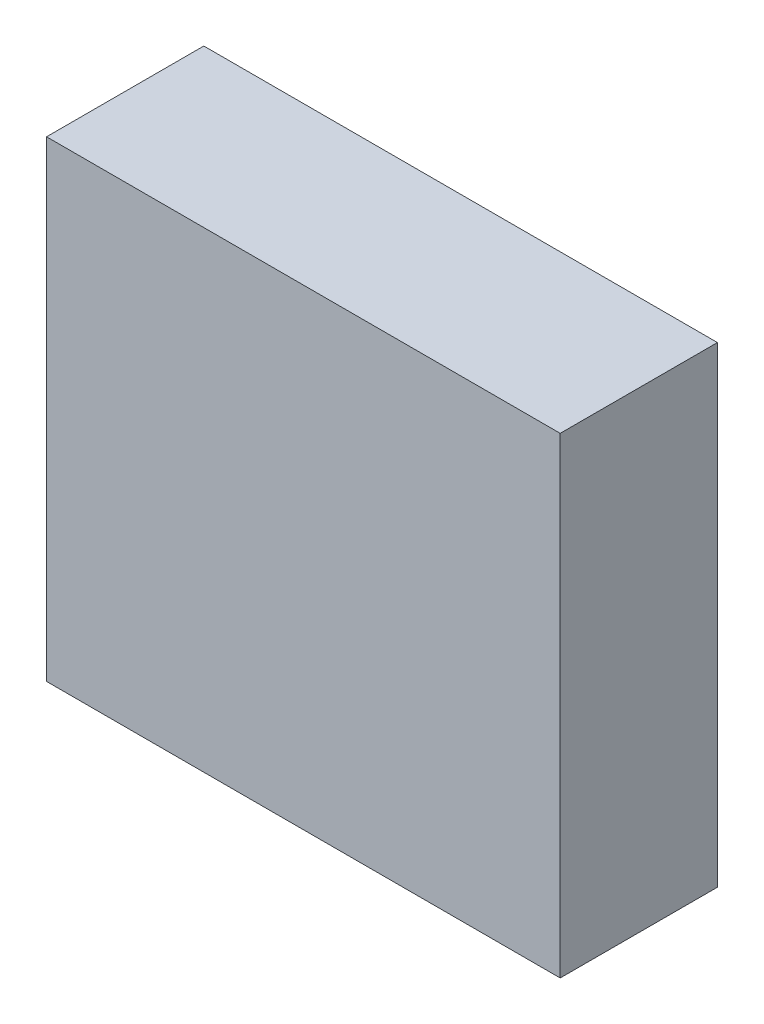
SolidWorks part; units mm, degrees
ref_plane "Plan de face" through (0, 0, 0) normal (0, 0, 1) x (1, 0, 0)
ref_plane "Plan de dessus" through (0, 0, 0) normal (0, 1, 0) x (1, 0, 0)
ref_plane "Plan de droite" through (0, 0, 0) normal (1, 0, 0) x (0, 0, -1)
sketch "Esquisse2" plane through (0, 0, 0) normal (0, 1, 0) x (1, 0, 0)
  line L1 (-49, -15) -> (49, -15)
  line L2 (-49, -15) -> (-49, 15)
  line L3 (-49, 15) -> (49, 15)
  line L4 (49, -15) -> (49, 15)
  line L5 (-49, -15) -> (49, 15) construction
  line L6 (-49, 15) -> (49, -15) construction
  point P0 (0, 0)
extrude "Boss.-Extru.1" add sketch "Esquisse2" along normal blind 90
